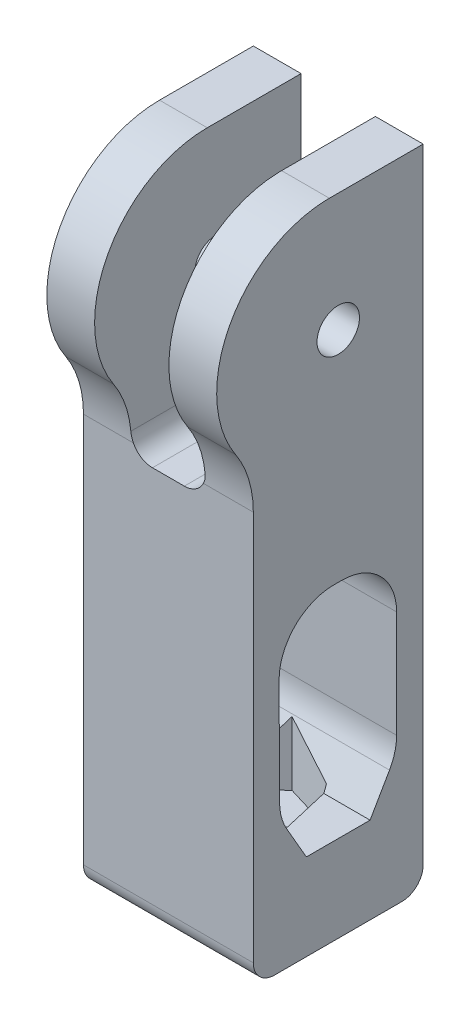
SolidWorks part; units mm, degrees
material "ABS generico"
ref_plane "Piano frontale" through (0, 0, 0) normal (0, 0, 1) x (1, 0, 0)
ref_plane "Piano superiore" through (0, 0, 0) normal (0, 1, 0) x (1, 0, 0)
ref_plane "Piano destro" through (0, 0, 0) normal (1, 0, 0) x (0, 0, -1)
sketch "Sketch9" plane through (0, 0, 0) normal (1, 0, 0) x (0, 0, -1)
  line L0 (8, 5.0539) -> (8, -49.642)
  line L1 (8, -49.642) -> (-8, -49.642)
  line L2 (-8, -49.642) -> (-8, -10.8758)
  line L3 (5.5, -41.5) -> (5.5, -25.7624)
  line L5 (0.3362, -20.5986) -> (-0.4104, -20.5986)
  line L6 (-5.5741, -25.7867) -> (-5.5, -41.5)
  line L7 (-5.5, -41.5) -> (5.5, -41.5)
  line L8 (0, -49.642) -> (0, 21.1385) construction
  circle A0 centre (0, 0) radius 2
  arc A1 (6.9253, 7.782) -> (-9.6743, -5.3367) centre (-0.8371, 0.5427) ccw
  arc A2 (-8, -10.8758) -> (-9.6743, -5.3367) centre (-18, -10.8758) ccw
  arc A3 (8, 5.0539) -> (6.9253, 7.782) centre (4, 5.0539) ccw
  arc A4 (5.5, -25.7624) -> (0.3362, -20.5986) centre (0.3362, -25.7624) ccw
  arc A5 (-5.5741, -25.7867) -> (-0.4104, -20.5986) centre (-0.4104, -25.7624) cw
  point P24 (8, 6.4221)
  dimension "D1" = 4
  dimension "D2" = 10
  dimension "D3" = 4
  dimension "D4" = 5.1638
  dimension "D5" = 16
extrude "Boss-Extrude3" add sketch "Sketch9" along normal blind 16
sketch "Sketch10" plane through (0, -49.642, 0) normal (0, -1, 0) x (1, 0, 0)
  line L0 (8, 8) -> (8, -8) construction
  line L1 (16, 8) -> (0, 8) construction
  line L2 (16, -8) -> (0, -8) construction
  line L3 (0, 0) -> (18.4029, 0) construction
  line L5 (0, 8) -> (0, -8) construction
  circle A0 centre (8, 0) radius 2
  point P11 (8, 0)
  dimension "D1" = 4
extrude "Cut-Extrude7" cut sketch "Sketch10" against normal blind 14
ref_plane "Plane1" through (0, 16, 0) normal (0, 1, 0) x (1, 0, 0)
sketch "Sketch11" plane through (0, 16, 0) normal (0, 1, 0) x (1, 0, 0)
  line L0 (8, 8) -> (8, -11.4514) construction
  line L1 (16, 8) -> (0, 8) construction
  line L2 (0, -11.4514) -> (16, -11.4514) construction
  line L4 (11.5, -16.0809) -> (4.5, -16.0809)
  line L5 (11.5, -16.0809) -> (11.5, 10.6052)
  line L6 (11.5, 10.6052) -> (4.5, 10.6052)
  line L7 (4.5, -16.0809) -> (4.5, 10.6052)
  line L8 (11.5, -16.0809) -> (4.5, 10.6052) construction
  line L9 (11.5, 10.6052) -> (4.5, -16.0809) construction
  point P6 (8, -2.7378)
  dimension "D1" = 7
extrude "Cut-Extrude8" cut sketch "Sketch11" against normal blind 28
fillet "Fillet1" radius 2 2 edges at (8, -49.642, -8) (8, -49.642, 8)
chamfer "Chamfer1" distance 2.5 angle 60 2 edges at (8, -41.5, 5.5) (8, -41.5, -5.5)
sketch "Sketch12" plane through (0, -41.5, 0) normal (0, 1, 0) x (1, 0, 0)
  line L1 (6.8952, 4.7506) -> (3.3335, 1.4185)
  line L2 (3.3335, 1.4185) -> (4.4383, -3.3321)
  line L3 (4.4383, -3.3321) -> (9.1048, -4.7506)
  line L4 (9.1048, -4.7506) -> (12.6665, -1.4185)
  line L5 (12.6665, -1.4185) -> (11.5617, 3.3321)
  line L6 (11.5617, 3.3321) -> (6.8952, 4.7506)
  circle A0 centre (8, 0) radius 4.8774 construction
extrude "Extrude1" cut sketch "Sketch12" against normal blind 3 and the other way blind 3
fillet "Fillet2" radius 2 2 edges at (4.5, -12, 0) (11.5, -12, 0)
fillet "Fillet3" radius 5 2 edges at (8, -37.1699, -5.5) (8, -37.1342, 5.5206)
sketch "Schizzo1" plane through (0, 0, 0) normal (-1, 0, 0) x (0, 0, 1)
  line L0 (0.8371, 11.157) -> (-8, 11.157)
  line L1 (-8, 4.2323) -> (-8, 11.157)
  line L2 (-8, -47.642) -> (-8, 5.0539) construction
  line L3 (-8, 4.2323) -> (1.127, 4.2323)
  line L4 (1.127, 4.2323) -> (0.8371, 11.157)
  arc A0 (9.6743, -5.3367) -> (-6.9253, 7.782) centre (0.8371, 0.5427) ccw construction
extrude "Estrusione-Estrusione1" add sketch "Schizzo1" against normal up to surface (4.5 mm away) up to face at (4.5, 0, 2)
sketch "Schizzo2" plane through (16, 0, 0) normal (1, 0, 0) x (0, 0, -1)
  line L0 (-0.8371, 11.157) -> (8, 11.157)
  line L1 (8, 11.157) -> (8, 3.9557)
  line L2 (8, -47.642) -> (8, 5.0539) construction
  line L3 (8, 3.9557) -> (-3.7709, 6.199)
  line L4 (-3.7709, 6.199) -> (-1.2125, 11.1504)
  line L5 (-1.2125, 11.1504) -> (-0.8371, 11.157)
  arc A0 (6.9253, 7.782) -> (-9.6743, -5.3367) centre (-0.8371, 0.5427) ccw construction
extrude "Estrusione-Estrusione2" add sketch "Schizzo2" against normal up to surface (4.5 mm away) up to face at (11.5, 0, -2)
